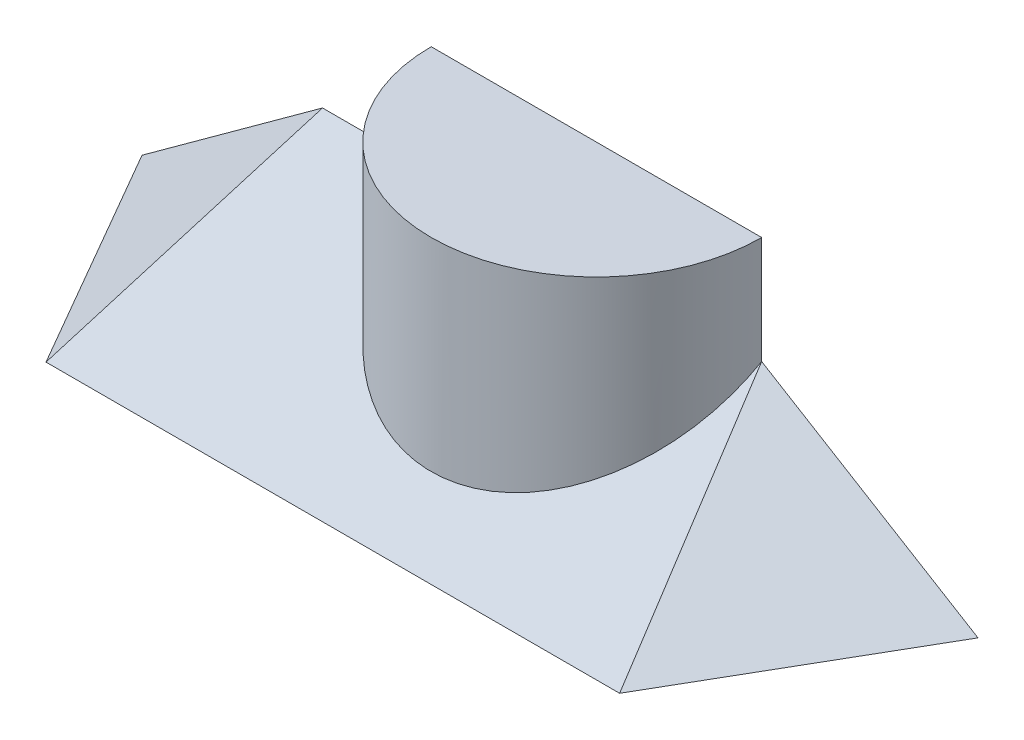
SolidWorks part; units mm, degrees
ref_plane "Front" through (0, 0, 0) normal (0, 0, 1) x (1, 0, 0)
ref_plane "Top" through (0, 0, 0) normal (0, 1, 0) x (1, 0, 0)
ref_plane "Right" through (0, 0, 0) normal (1, 0, 0) x (0, 0, -1)
sketch "Sketch1" plane through (0, 0, 0) normal (0, 1, 0) x (1, 0, 0)
  line L0 (40, 0) -> (-40, 0)
  line L1 (-40, 0) -> (-110, 0) construction
  line L2 (-110, 0) -> (-78.2457, -55) construction
  line L3 (-78.2457, -55) -> (-108.717, -55) construction
  line L4 (-78.2457, -55) -> (120.1791, -55) construction
  line L5 (40, 0) -> (112.1068, 0) construction
  line L6 (105.1449, 12.9732) -> (56.093, -71.9872) construction
  arc A0 (-40, 0) -> (40, 0) centre (0, 0) ccw
  dimension "D1" = 70
  dimension "D2" = 60
  dimension "D3" = 55
  dimension "D4" = 60
sketch "Sketch2" plane through (0, 0, 0) normal (1, 0, 0) x (0, 0, -1)
  line L0 (0, 0) -> (0, 31.7543)
  line L1 (0, 31.7543) -> (-55, 0)
  line L2 (12.9732, 0) -> (-71.9872, 0) construction
  line L3 (0, 0) -> (-55, 0) construction
  line L4 (-55, 0) -> (0, 0)
  dimension "D1" = 55
  dimension "D2" = 30
extrude "Extrude1" add sketch "Sketch2" against normal blind 78.25 and the other way blind 40
ref_plane "Plane1" through (-110, 0, 0) normal (0.5, 0, 0.866) x (0.866, 0, -0.5)
ref_plane "Plane2" through (-11.6225, 0, -20.1308) normal (0.5, 0, 0.866) x (0.866, 0, -0.5)
sketch "Sketch4" plane through (-11.6225, 0, -20.1308) normal (0.5, 0, 0.866) x (0.866, 0, -0.5)
  line L0 (-95.2665, 0) -> (-57.4232, 31.7543)
  line L1 (-57.4232, 31.7543) -> (-57.4232, 0)
  line L3 (-34.641, 0) -> (-95.2628, 0) construction
  line L4 (-57.4232, 0) -> (-95.2665, 0)
  dimension "D1" = 40
extrude "Extrude2" add sketch "Sketch4" along normal mid plane 63.51
ref_plane "Plane3" through (56.093, 0, 71.9872) normal (-0.5, 0, 0.866) x (0.866, 0, 0.5)
ref_plane "Plane4" through (-1.2706, 0, 2.2008) normal (-0.5, 0, 0.866) x (0.866, 0, 0.5)
sketch "Sketch6" plane through (-1.2706, 0, 2.2008) normal (-0.5, 0, 0.866) x (0.866, 0, 0.5)
  line L0 (34.641, 31.7543) -> (79.9908, 0)
  line L1 (34.641, 31.7543) -> (34.641, 0)
  line L2 (34.641, 0) -> (79.9908, 0)
  dimension "D1" = 35
extrude "Extrude4" add sketch "Sketch6" along normal mid plane 103.51
sketch "Sketch7" plane through (-34.0883, 46.9096, 19.6809) normal (-0.5567, 0.766, 0.3214) x (-0.8307, -0.5133, -0.2154)
  line L0 (51.932, -29.7316) -> (91.3829, 0.0017) construction
  line L1 (16.9734, 59.873) -> (67.7361, 59.873)
  line L2 (16.9734, 59.873) -> (16.9734, -17.8204)
  line L3 (16.9734, -17.8204) -> (67.7361, -17.8204)
  line L4 (67.7361, 59.873) -> (67.7361, -17.8204)
extrude "Cut-Extrude1" cut sketch "Sketch7" along normal blind 10
sketch "Sketch8" plane through (0, 23.8157, 13.75) normal (0, 0.866, 0.5) x (-1, 0, 0)
  line L1 (-83.0034, -51.2638) -> (97.5396, -51.2638)
  line L2 (-83.0034, -51.2638) -> (-83.0034, 79.055)
  line L3 (-83.0034, 79.055) -> (97.5396, 79.055)
  line L4 (97.5396, -51.2638) -> (97.5396, 79.055)
extrude "Cut-Extrude2" cut sketch "Sketch8" along normal blind 40
sketch "Sketch9" plane through (0, 0, 0) normal (0, 1, 0) x (1, 0, 0)
  line L1 (-110.0032, -0.0018) -> (103.4656, -0.0018)
  line L2 (-110.0032, -0.0018) -> (-110.0032, 29.3725)
  line L3 (-110.0032, 29.3725) -> (103.4656, 29.3725)
  line L4 (103.4656, -0.0018) -> (103.4656, 29.3725)
extrude "Cut-Extrude3" cut sketch "Sketch9" along normal through all
extrude "Extrude5" add sketch "Sketch1" along normal blind 57.75
ref_plane "AB Dihedral Angle Plane" through (-72.2785, 15.8766, 27.5009) normal (0.1848, 0.4914, -0.8511) x (-0.9828, 0.0924, -0.1601)
